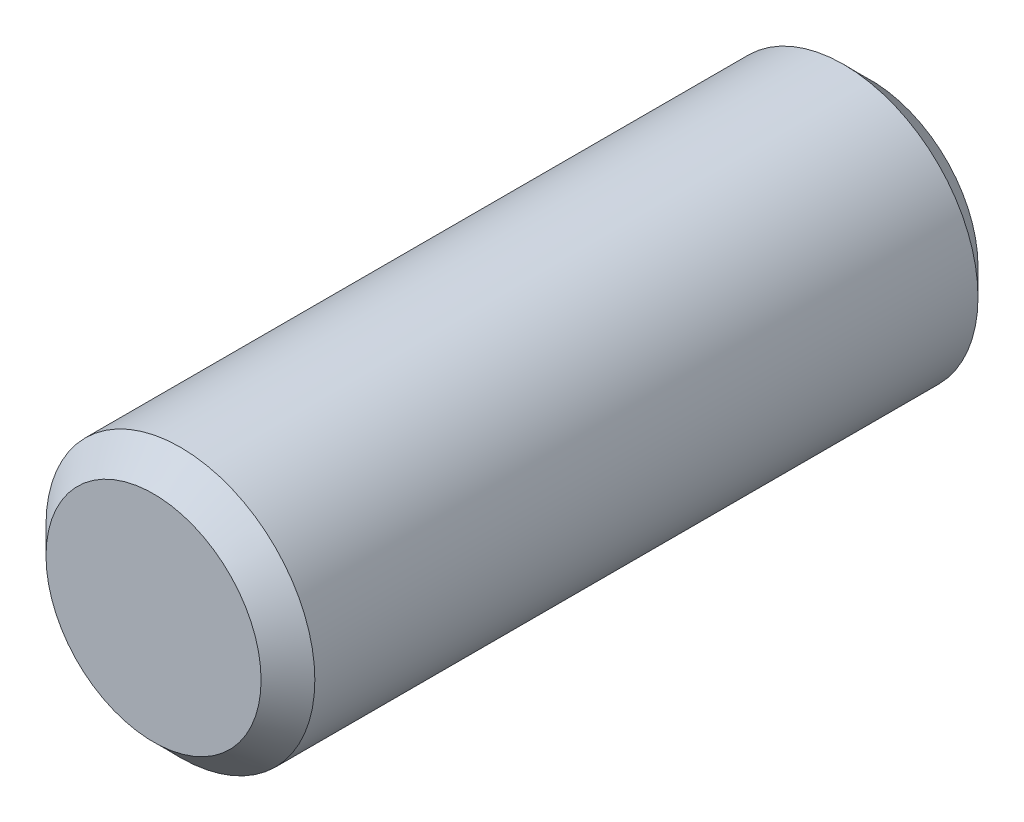
SolidWorks part; units mm, degrees
ref_plane "前视基准面" through (0, 0, 0) normal (0, 0, 1) x (1, 0, 0)
ref_plane "上视基准面" through (0, 0, 0) normal (0, 1, 0) x (1, 0, 0)
ref_plane "右视基准面" through (0, 0, 0) normal (1, 0, 0) x (0, 0, -1)
sketch "草图1" plane through (0, 0, 0) normal (0, 0, 1) x (1, 0, 0)
  circle A0 centre (0, 0) radius 1.5
extrude "凸台-拉伸1" add sketch "草图1" along normal blind 8
chamfer "倒角1" distance 0.3 angle 45 2 edges at (1.5, 0, 8) (1.5, 0, 0)
